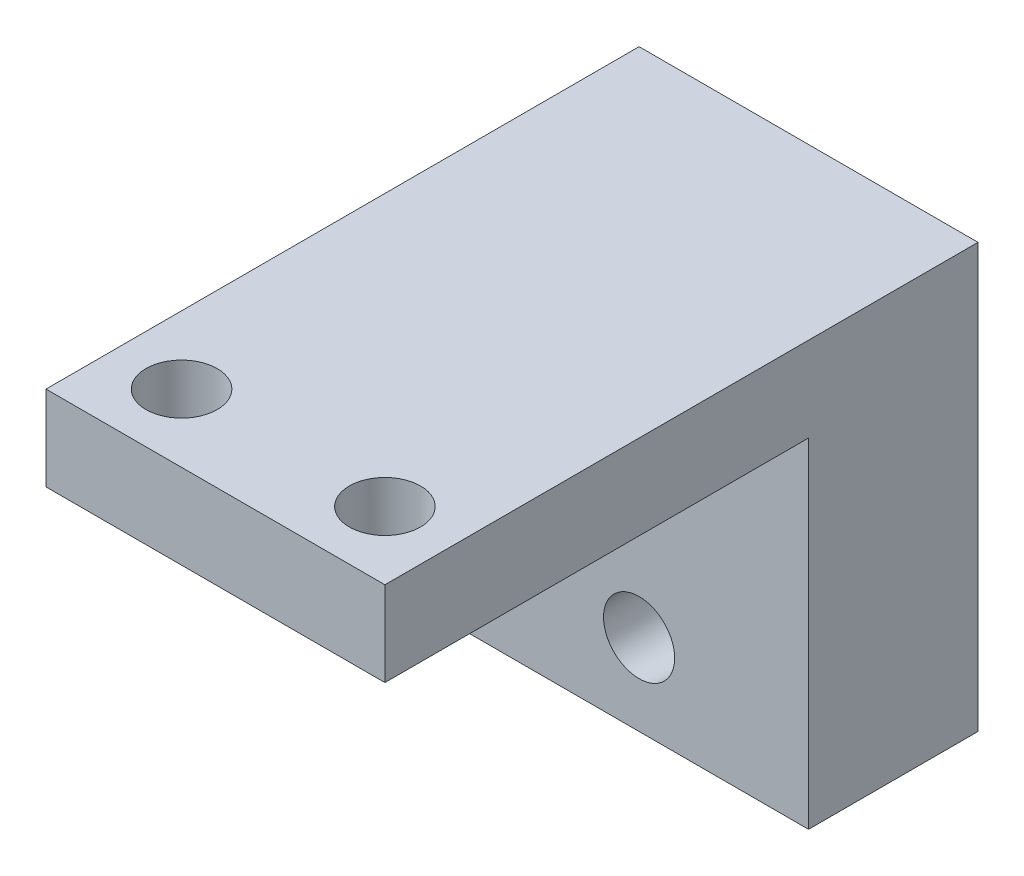
SolidWorks part; units mm, degrees
ref_plane "前视基准面" through (0, 0, 0) normal (0, 0, 1) x (1, 0, 0)
ref_plane "上视基准面" through (0, 0, 0) normal (0, 1, 0) x (1, 0, 0)
ref_plane "右视基准面" through (0, 0, 0) normal (1, 0, 0) x (0, 0, -1)
other "Configuration Table"
sketch "草图1" plane through (0, 0, 0) normal (0, 0, 1) x (1, 0, 0)
  line L1 (10, -10) -> (-10, -10)
  line L2 (10, -10) -> (10, 10)
  line L3 (10, 10) -> (-10, 10)
  line L4 (-10, -10) -> (-10, 10)
  line L5 (10, -10) -> (-10, 10) construction
  line L6 (10, 10) -> (-10, -10) construction
  circle A0 centre (0, 5.2) radius 2.1
  circle A1 centre (0, -5.2) radius 2.1
  point P0 (0, 0)
  dimension "D5" = 4.2
  dimension "D6" = 4.2
  dimension "D1" = 20
  dimension "D2" = 20
  dimension "D3" = 4.8
  dimension "D4" = 4.8
extrude "凸台-拉伸1" add sketch "草图1" along normal blind 10 contours A1 | A0 | L3 L4 L1 L2
sketch "草图2" plane through (0, 10, 0) normal (0, 1, 0) x (1, 0, 0)
  line L1 (-10, 0) -> (10, 0)
  line L2 (-10, 0) -> (-10, -10)
  line L3 (-10, -10) -> (10, -10)
  line L4 (10, 0) -> (10, -10)
extrude "凸台-拉伸2" add sketch "草图2" along normal blind 5
sketch "草图3" plane through (0, 0, 10) normal (0, 0, 1) x (1, 0, 0)
  line L0 (10, -10) -> (10, 15) construction
  line L1 (-10, 15) -> (10, 15)
  line L2 (-10, 15) -> (-10, 10)
  line L3 (-10, 10) -> (10, 10)
  line L4 (10, 15) -> (10, 10)
  dimension "D1" = 5
extrude "凸台-拉伸3" add sketch "草图3" along normal blind 25
sketch "草图4" plane through (0, 10, 0) normal (0, -1, 0) x (1, 0, 0)
  line L0 (-10, 35) -> (10, 35) construction
  line L1 (-10, 35) -> (-10, 10) construction
  line L2 (10, 35) -> (10, 10) construction
  circle A0 centre (-6, 31) radius 2.1
  circle A1 centre (6, 31) radius 2.1
  dimension "D2" = 4.2
  dimension "D5" = 4.2
  dimension "D1" = 4
  dimension "D3" = 4
  dimension "D4" = 4
  dimension "D6" = 12
extrude "切除-拉伸1" cut sketch "草图4" against normal blind 25
